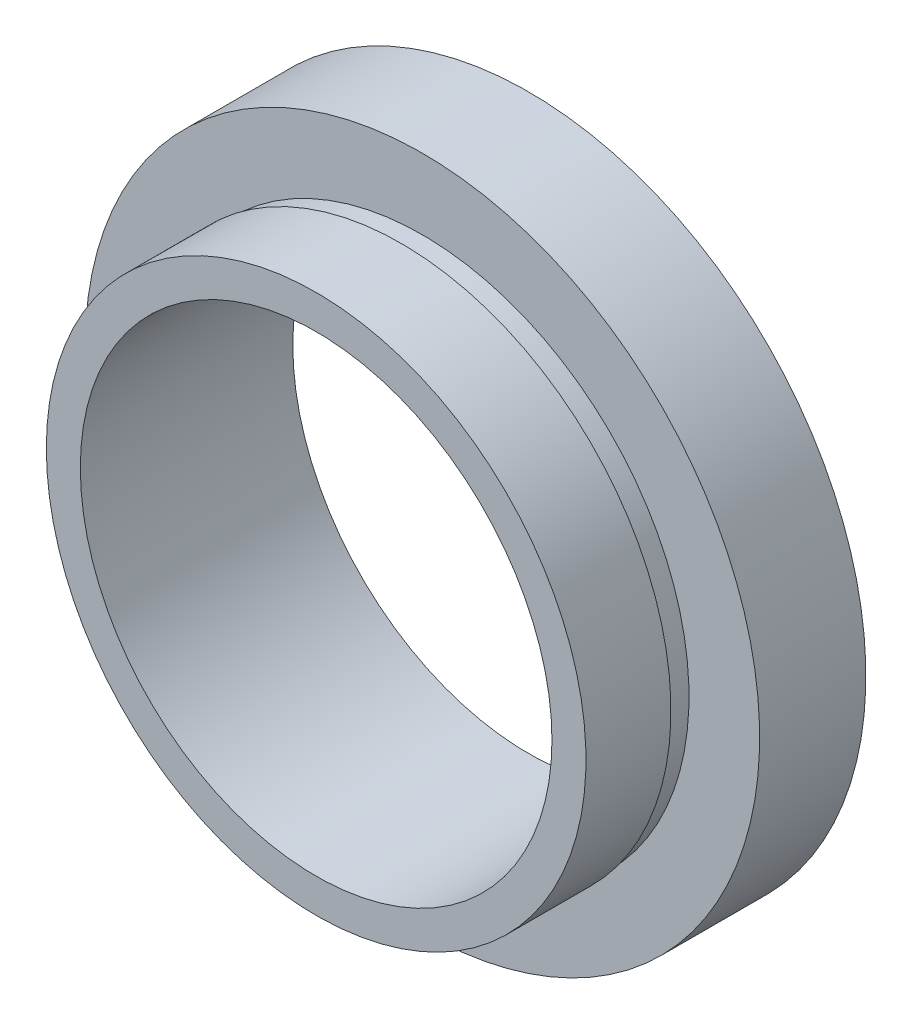
SolidWorks part; units mm, degrees
ref_plane "前视基准面" through (0, 0, 0) normal (0, 0, 1) x (1, 0, 0)
ref_plane "上视基准面" through (0, 0, 0) normal (0, 1, 0) x (1, 0, 0)
ref_plane "右视基准面" through (0, 0, 0) normal (1, 0, 0) x (0, 0, -1)
sketch "草图1" plane through (0, 0, 0) normal (0, 1, 0) x (1, 0, 0)
  line L0 (0, 19.1406) -> (0, -28.4043) construction
  line L1 (11.1, 0) -> (11.1, 10)
  line L2 (11.1, 0) -> (12.7, 0)
  line L3 (12.7, 0) -> (12.7, 4)
  line L4 (12.7, 4) -> (12.55, 4)
  line L5 (12.55, 4) -> (12.55, 5)
  line L6 (12.55, 5) -> (15.875, 5)
  line L7 (15.875, 5) -> (15.875, 10)
  line L8 (15.875, 10) -> (11.1, 10)
  dimension "D3" = 12.55
  dimension "D1" = 11.1
  dimension "D2" = 12.7
  dimension "D4" = 15.875
  dimension "D5" = 1
  dimension "D6" = 5
  dimension "D7" = 10
revolve "旋转1" add sketch "草图1" angle 360 about L0
cosmetic thread "装饰螺纹线1"
cosmetic thread "装饰螺纹线2"
